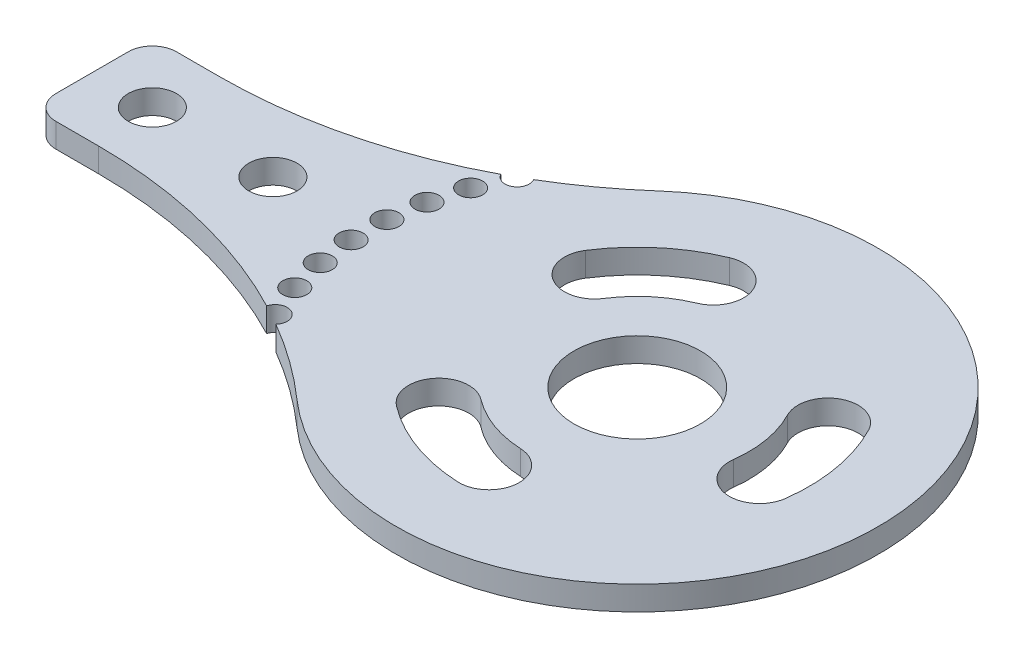
SolidWorks part; units mm, degrees
material "Стеклотекстолит"
ref_plane "Спереди" through (0, 0, 0) normal (0, 0, 1) x (1, 0, 0)
ref_plane "Сверху" through (0, 0, 0) normal (0, 1, 0) x (1, 0, 0)
ref_plane "Справа" through (0, 0, 0) normal (1, 0, 0) x (0, 0, -1)
sketch "Эскиз1" plane through (0, 0, 0) normal (0, 1, 0) x (1, 0, 0)
  line L0 (0, -2) -> (0, -8)
  line L1 (2, -10) -> (5.5425, -10)
  line L2 (2, 0) -> (5.5425, 0)
  line L3 (5.5425, 0) -> (5.5425, -10) construction
  arc A0 (32, -20) -> (32, 10) centre (45.2288, -5) ccw
  arc A1 (5.5425, -10) -> (32, -20) centre (5.5425, -50) cw
  arc A2 (5.5425, 0) -> (32, 10) centre (5.5425, 40) ccw
  arc A3 (0, -8) -> (2, -10) centre (2, -8) ccw
  arc A4 (0, -2) -> (2, 0) centre (2, -2) cw
  point P12 (0, -10)
  point P15 (0, 0)
  dimension "D2" = 40
  dimension "D3" = 2
  dimension "D4" = 20
  dimension "D1" = 10
  dimension "D5" = 32
extrude "Бобышка-Вытянуть1" add sketch "Эскиз1" along normal blind 2
sketch "Эскиз2" plane through (0, 2, 0) normal (0, 1, 0) x (1, 0, 0)
  circle A2 centre (25.1372, 5.1281) radius 1
  circle A4 centre (45.2288, -5) radius 22.5 construction
  arc A5 (32, -20) -> (32, 10) centre (45.2288, -5) ccw construction
  arc A6 (5.5425, 0) -> (32, 10) centre (5.5425, 40) ccw construction
  dimension "D1" = 2
  dimension "D2" = 45
extrude "Вырез-Вытянуть1" cut sketch "Эскиз2" against normal through all
pattern_circular "Круговой массив1" count 8 every 7.5 about axis through (45.2288, 0, 5) along (0, 1, 0) of "Вырез-Вытянуть1"
sketch "Эскиз3" plane through (0, 2, 0) normal (0, 1, 0) x (1, 0, 0)
  line L0 (0, -2) -> (0, -8) construction
  line L3 (5, -10) -> (5, 0) construction
  line L4 (2, -10) -> (5.5425, -10) construction
  line L5 (5.5425, 0) -> (2, 0) construction
  circle A0 centre (5, -5) radius 2
  dimension "D1" = 4
  dimension "D2" = 5
extrude "Вырез-Вытянуть2" cut sketch "Эскиз3" against normal through all
pattern_linear "Линейный массив1" count 2 spacing 10 along (1, 0, 0) of "Вырез-Вытянуть2"
sketch "Эскиз4" plane through (0, 2, 0) normal (0, 1, 0) x (1, 0, 0)
  circle A0 centre (45.2288, -5) radius 11.75 construction
  arc A1 (32, -20) -> (32, 10) centre (45.2288, -5) ccw construction
  circle A2 centre (45.2288, 6.75) radius 2
  dimension "D1" = 4
  dimension "D2" = 23.5
extrude "Вырез-Вытянуть3" [suppressed] cut sketch "Эскиз4" against normal through all
pattern_circular "Круговой массив2" [suppressed] count 8 every 45
sketch "Эскиз6" plane through (0, 2, 0) normal (0, 1, 0) x (1, 0, 0)
  line L0 (45.2288, -5) -> (34.7269, 5.5019) construction
  line L1 (45.2288, -5) -> (35.4788, -5) construction
  arc A0 (41.6704, 3.5381) -> (37.4462, -0.0008) centre (45.2288, -5) ccw
  arc A1 (32, -20) -> (32, 10) centre (45.2288, -5) ccw construction
  arc A2 (39.747, 8.1533) -> (33.2394, 2.7016) centre (45.2288, -5) ccw
  circle A4 centre (35.3428, 1.3504) radius 2.5
  circle A5 centre (40.7087, 5.8457) radius 2.5
  circle M8 centre (15, -5) radius 2
  dimension "D1" = 5
  dimension "D2" = 5
  dimension "D3" = 45
  dimension "D4" = 11.7499
  dimension "D5" = 7
extrude "Вырез-Вытянуть4" cut sketch "Эскиз6" against normal through all contours A4 | A5 A2 A4 A0 | A5 M8
pattern_circular "Круговой массив3" count 3 every 120 about axis through (45.2288, 0, 5) along (0, 1, 0) of "Вырез-Вытянуть4"
sketch "Эскиз7" plane through (0, 2, 0) normal (0, 1, 0) x (1, 0, 0)
  circle A0 centre (45.2288, -5) radius 5.25
  arc A1 (32, -20) -> (32, 10) centre (45.2288, -5) ccw construction
  dimension "D1" = 10.5
extrude "Вырез-Вытянуть5" cut sketch "Эскиз7" against normal through all
equation "\"thick\"= \"thick@балка.SLDASM\""
equation "\"D1@Бобышка-Вытянуть1\"=\"thick\""
